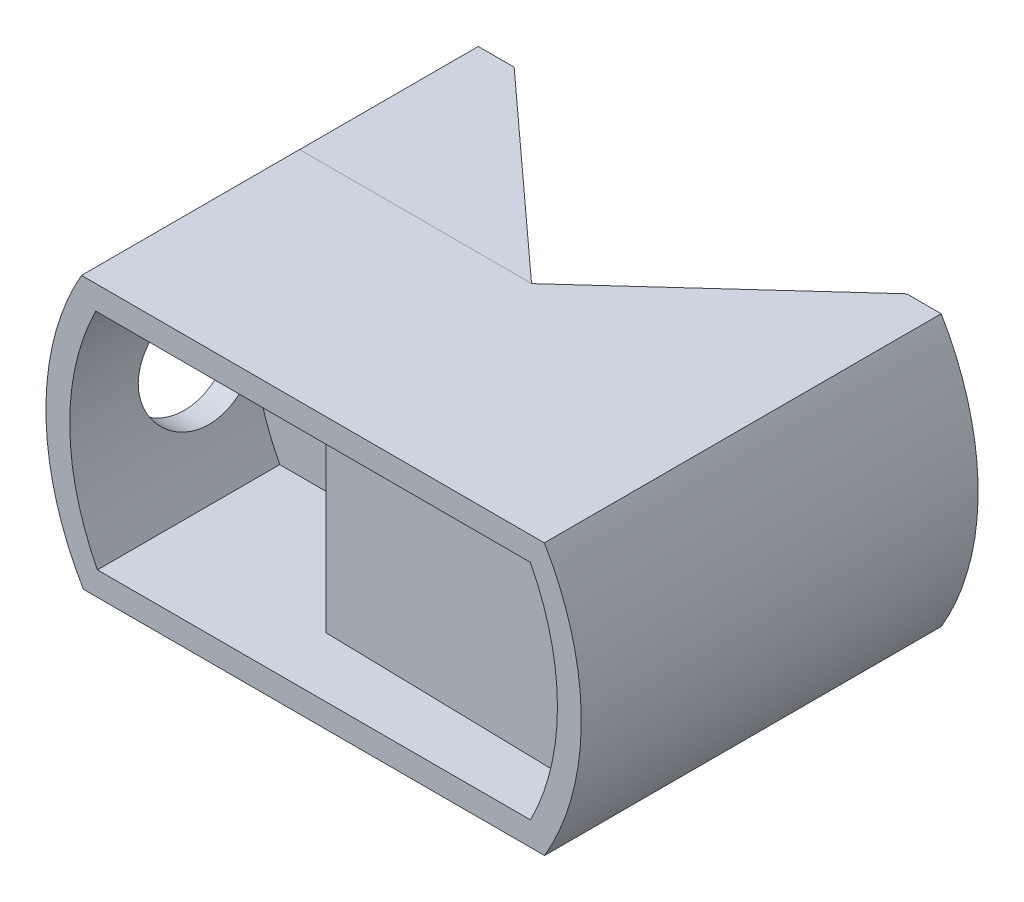
SolidWorks part; units mm, degrees
ref_plane "Front Plane" through (0, 0, 0) normal (0, 0, 1) x (1, 0, 0)
ref_plane "Top Plane" through (0, 0, 0) normal (0, 1, 0) x (1, 0, 0)
ref_plane "Right Plane" through (0, 0, 0) normal (1, 0, 0) x (0, 0, -1)
sketch "Sketch1" plane through (0, 0, -12.295) normal (0, 0, -1) x (-1, 0, 0)
  line L4 (-169.3691, -111.49) -> (-130.6784, -111.4894)
  line L5 (-130.5221, -88.7593) -> (-169.3507, -88.7786)
  line L6 (-169.3691, -111.49) -> (-130.6784, -111.4894)
  line L7 (-130.5221, -88.7593) -> (-169.3507, -88.7786)
  arc A4 (-130.6784, -111.4894) -> (-130.5221, -88.7593) centre (-150.13, -99.99) ccw
  arc A5 (-169.3507, -88.7786) -> (-169.3691, -111.49) centre (-150.04, -100.15) ccw
  arc A6 (-130.6784, -111.4894) -> (-130.5221, -88.7593) centre (-150.13, -99.99) ccw
  arc A7 (-169.3507, -88.7786) -> (-169.3691, -111.49) centre (-150.04, -100.15) ccw
  dimension "D1" = 2.5
extrude "Boss-Extrude1" add sketch "Sketch1" against normal offset from surface (15.295 mm away) 3
sketch "Sketch2" plane through (0, 0, 3) normal (0, 0, 1) x (1, 0, 0)
  line L4 (168.1711, -90.7781) -> (131.7176, -90.7599)
  line L5 (131.855, -109.4894) -> (168.1876, -109.49)
  line L6 (168.1711, -90.7781) -> (131.7176, -90.7599)
  line L7 (131.855, -109.4894) -> (168.1876, -109.49)
  arc A4 (168.1876, -109.49) -> (168.1711, -90.7781) centre (150.04, -100.15) ccw
  arc A5 (131.7176, -90.7599) -> (131.855, -109.4894) centre (150.13, -99.99) ccw
  arc A6 (168.1876, -109.49) -> (168.1711, -90.7781) centre (150.04, -100.15) ccw
  arc A7 (131.7176, -90.7599) -> (131.855, -109.4894) centre (150.13, -99.99) ccw
  dimension "D1" = 2
extrude "Cut-Extrude1" cut sketch "Sketch2" against normal through all
sketch "Sketch4" plane through (0, 0, -12.295) normal (0, 0, -1) x (-1, 0, 0)
  line L2 (-169.3691, -111.49) -> (-130.6784, -111.4894)
  line L3 (-130.5221, -88.7593) -> (-169.3507, -88.7786)
  line L4 (-169.3691, -111.49) -> (-130.6784, -111.4894)
  line L5 (-130.5221, -88.7593) -> (-169.3507, -88.7786)
  arc A2 (-169.3507, -88.7786) -> (-169.3691, -111.49) centre (-150.04, -100.15) ccw
  arc A3 (-130.6784, -111.4894) -> (-130.5221, -88.7593) centre (-150.13, -99.99) ccw
  arc A4 (-169.3507, -88.7786) -> (-169.3691, -111.49) centre (-150.04, -100.15) ccw
  arc A5 (-130.6784, -111.4894) -> (-130.5221, -88.7593) centre (-150.13, -99.99) ccw
  dimension "D1" = 0
extrude "floor" add sketch "Sketch4" along normal blind 3
sketch "Sketch6" plane through (0, 0, -12.295) normal (0, 0, 1) x (1, 0, 0)
  line L0 (146.5, -90.7672) -> (146.5, -108.9896)
  line L1 (167.88, -108.99) -> (132.1612, -108.9894) construction
  line L2 (131.855, -109.4894) -> (168.1876, -109.49)
  line L3 (168.1711, -90.7781) -> (131.7176, -90.7599)
  line L6 (145, -95.6) -> (145, -104.4) construction
  line L7 (168.1711, -90.7781) -> (146.5, -90.7672)
  line L8 (168.1876, -109.49) -> (146.5, -108.9896)
  arc A2 (168.1876, -109.49) -> (168.1711, -90.7781) centre (150.04, -100.15) ccw
  arc A3 (131.7176, -90.7599) -> (131.855, -109.4894) centre (150.13, -99.99) ccw
  arc A4 (168.1876, -109.49) -> (168.1711, -90.7781) centre (150.04, -100.15) ccw
  dimension "D2" = 1.5
  dimension "D1" = 0
extrude "Boss-Extrude4" add sketch "Sketch6" along normal offset from surface (10.775 mm away) 0.01
sketch "Sketch9" plane through (0, 0, -15.295) normal (0, 0, -1) x (-1, 0, 0)
  line L0 (-169.3507, -88.7786) -> (-130.6784, -111.4894) construction
  line L1 (-130.5221, -88.7593) -> (-169.3691, -111.49) construction
  line L2 (-169.3691, -111.49) -> (-130.6784, -111.4894)
  line L3 (-130.5221, -88.7593) -> (-169.3507, -88.7786)
  line L4 (-169.3691, -111.49) -> (-130.6784, -111.4894)
  line L5 (-130.5221, -88.7593) -> (-169.3507, -88.7786)
  arc A2 (-169.3507, -88.7786) -> (-169.3691, -111.49) centre (-150.04, -100.15) ccw
  arc A3 (-130.6784, -111.4894) -> (-130.5221, -88.7593) centre (-150.13, -99.99) ccw
  arc A4 (-169.3507, -88.7786) -> (-169.3691, -111.49) centre (-150.04, -100.15) ccw
  arc A5 (-130.6784, -111.4894) -> (-130.5221, -88.7593) centre (-150.13, -99.99) ccw
  point P0 (-149.9882, -100.1495)
  point P5 (0, 0)
  point P8 (0, 0)
  point P9 (0, 0)
  point P10 (0, 0)
  dimension "D1" = 0
ref_plane "Plane1" through (0, 0, -15.295) normal (0, 0, -1) x (-1, 0, 0)
ref_plane "Plane2" through (149.9898, -0.0025, 0) normal (-1, 0, 0) x (0, 0, 1)
sketch "Sketch11" plane through (-0.0443, -88.694, 0) normal (0.0005, 1, 0) x (1, -0.0005, 0)
  line L0 (150.0382, 15.295) -> (166.5001, 30.295)
  line L1 (166.5001, 30.295) -> (172.5001, 30.295)
  line L2 (172.5001, 30.295) -> (172.5001, 15.295)
  line L3 (172.5001, 15.295) -> (169.395, 15.295) construction
  line L4 (12.5019, 15.295) -> (-12.5019, 15.295) construction
  line L5 (172.5001, 15.295) -> (150.0382, 15.295)
  line L12 (172.5001, -3) -> (172.5001, 15.295) construction
  dimension "D1" = 15
  dimension "D2" = 6
extrude "Boss-Extrude5" add sketch "Sketch11" against normal up to surface (22.7099 mm away)
sketch "Sketch7" plane through (0, 0, 0) normal (1, 0, 0) x (0, 0, -1)
  circle A0 centre (7.995, -100) radius 5.25
  dimension "D1" = 10.5
extrude "Cut-Extrude3" cut sketch "Sketch7" along normal up to surface (146.5 mm away) up to face at (146.5, -99.8784, -6.9075)
mirror "Mirror1" about plane through (149.9898, -0.0025, 0) normal (-1, 0, 0) of "Boss-Extrude5"
sketch "Sketch14" plane through (0, 0, 3) normal (0, 0, 1) x (1, 0, 0)
  line L2 (169.3507, -88.7786) -> (130.5221, -88.7593)
  line L3 (130.6784, -111.4894) -> (169.3691, -111.49)
  line L4 (169.3507, -88.7786) -> (130.5221, -88.7593)
  line L5 (130.6784, -111.4894) -> (169.3691, -111.49)
  arc A2 (169.3691, -111.49) -> (169.3507, -88.7786) centre (150.04, -100.15) ccw
  arc A3 (130.5221, -88.7593) -> (130.6784, -111.4894) centre (150.13, -99.99) ccw
  arc A4 (169.3691, -111.49) -> (169.3507, -88.7786) centre (150.04, -100.15) ccw
  arc A5 (130.5221, -88.7593) -> (130.6784, -111.4894) centre (150.13, -99.99) ccw
  dimension "D1" = 0
extrude "Cut-Extrude4" cut sketch "Sketch14" against normal up to surface (33.295 mm away) flip side to cut up to face at (169.4501, -100.1344, -30.295)
ref_point "Point1"
move or copy body "Body-Move/Copy1" bodies to move or copy 110 copy no translate (-149.9882, 100.1495, 15.295)
